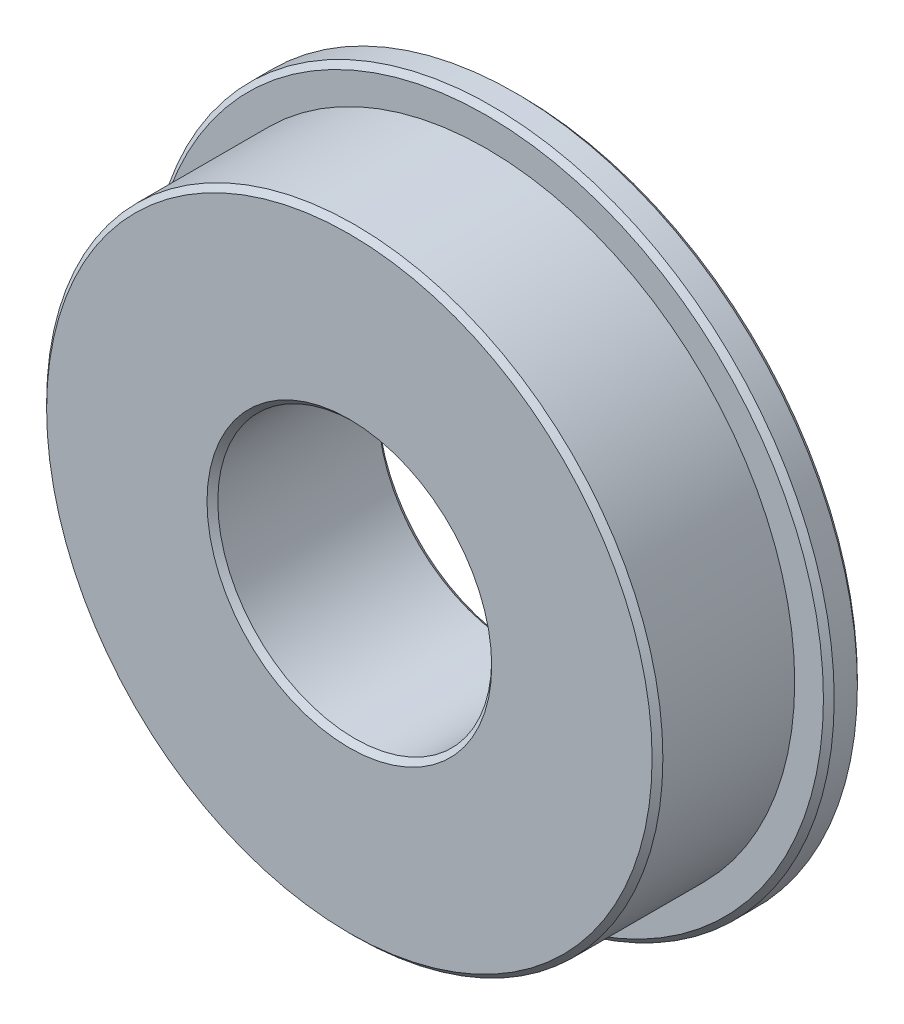
SolidWorks part; units mm, degrees
material "PVC 0.007 Plasticized"
ref_plane "Front Plane" through (0, 0, 0) normal (0, 0, 1) x (1, 0, 0)
ref_plane "Top Plane" through (0, 0, 0) normal (0, 1, 0) x (1, 0, 0)
ref_plane "Right Plane" through (0, 0, 0) normal (1, 0, 0) x (0, 0, -1)
sketch "Sketch1" plane through (0, 0, 0) normal (0, 1, 0) x (1, 0, 0)
  line L0 (0, 0) -> (0, 6.8644) construction
  line L1 (-14.2875, 6.3627) -> (-14.2875, 0)
  line L2 (-14.2875, 0) -> (-6.35, 0)
  line L3 (-6.35, 0) -> (-6.35, 7.9375)
  line L4 (-6.35, 7.9375) -> (-15.8688, 7.9375)
  line L5 (-15.8688, 7.9375) -> (-15.8688, 6.3627)
  line L6 (-15.8688, 6.3627) -> (-14.2875, 6.3627)
  dimension "D1" = 12.7
  dimension "D2" = 28.575
  dimension "D3" = 7.9375
  dimension "D4" = 6.3627
  dimension "D5" = 31.7375
revolve "Revolve1" add sketch "Sketch1" angle 360 about L0
chamfer "Chamfer1" distance 0.25 angle 45 5 edges at (6.35, 0, 0) (14.2875, 0, 0) (6.35, 0, -7.9375) (15.8688, 0, -7.9375) (15.8688, 0, -6.3627)
